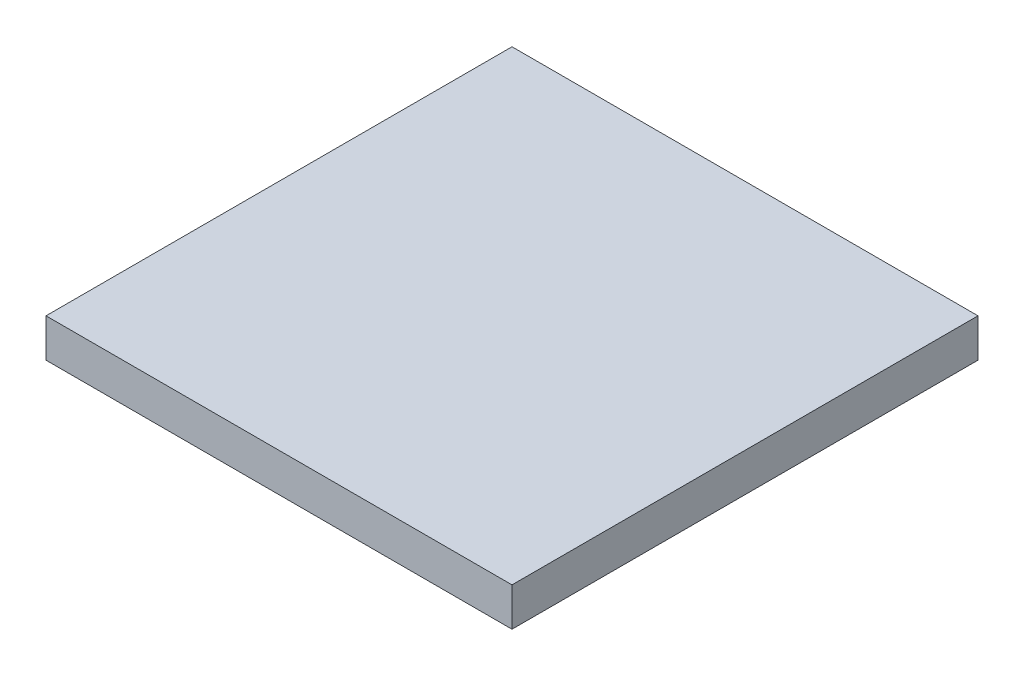
SolidWorks part; units mm, degrees
ref_plane "Front Plane" through (0, 0, 0) normal (0, 0, 1) x (1, 0, 0)
ref_plane "Top Plane" through (0, 0, 0) normal (0, 1, 0) x (1, 0, 0)
ref_plane "Right Plane" through (0, 0, 0) normal (1, 0, 0) x (0, 0, -1)
sketch "Sketch1" plane through (0, 0, 0) normal (0, 1, 0) x (1, 0, 0)
  line L1 (-20, -20) -> (20, -20)
  line L2 (-20, -20) -> (-20, 20)
  line L3 (-20, 20) -> (20, 20)
  line L4 (20, -20) -> (20, 20)
  line L5 (-20, -20) -> (20, 20) construction
  line L6 (-20, 20) -> (20, -20) construction
  point P0 (0, 0)
  dimension "D1" = 40
  dimension "D2" = 40
extrude "Boss-Extrude1" add sketch "Sketch1" along normal blind 3.3
